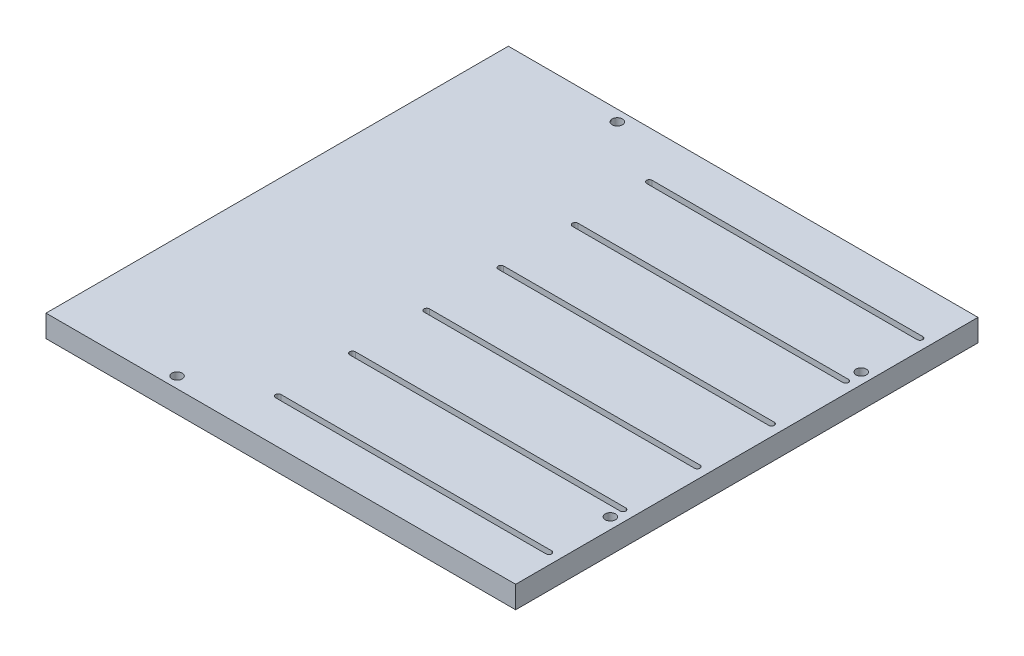
SolidWorks part; units mm, degrees
material "Acrylic (Medium-high impact)"
ref_plane "Front Plane" through (0, 0, 0) normal (0, 0, 1) x (1, 0, 0)
ref_plane "Top Plane" through (0, 0, 0) normal (0, 1, 0) x (1, 0, 0)
ref_plane "Right Plane" through (0, 0, 0) normal (1, 0, 0) x (0, 0, -1)
other "Configuration Table"
sketch "Sketch1" plane through (0, 0, 0) normal (0, 1, 0) x (1, 0, 0)
  line L1 (-42, -66.35) -> (42, -66.35)
  line L2 (-42, -66.35) -> (-42, 66.35) construction
  line L3 (-42, 66.35) -> (42, 66.35)
  line L4 (42, -66.35) -> (42, 66.35)
  line L5 (-42, -66.35) -> (42, 66.35) construction
  line L6 (-42, 66.35) -> (42, -66.35) construction
  line L7 (-42, 66.35) -> (-92.8, 66.35)
  line L9 (-42, -66.35) -> (-92.8, -66.35)
  line L10 (-92.8, 66.35) -> (-92.8, -66.35)
  point P0 (0, 0)
  dimension "D1" = 84
  dimension "D2" = 132.7
  dimension "D3" = 50.8
extrude "Boss-Extrude1" add sketch "Sketch1" along normal blind 6.35
sketch "Sketch2" plane through (0, 6.35, 0) normal (0, 1, 0) x (1, 0, 0)
  line L0 (38.825, -66.35) -> (38.825, 66.35) construction
  line L1 (-92.8, -66.35) -> (42, -66.35) construction
  line L2 (42, 66.35) -> (-92.8, 66.35) construction
  line L3 (42, -66.35) -> (42, 66.35) construction
  line L4 (-42, 0) -> (42, 0) construction
  line L6 (-42, -66.35) -> (-42, 66.35) construction
  circle A0 centre (38.825, -35.997) radius 1.4732
  circle A2 centre (38.825, 35.997) radius 1.4732
  point P12 (0, 0)
  dimension "D2" = 30.353
  dimension "D3" = 2.9464
  dimension "D1" = 3.175
sketch "Sketch4" plane through (0, 6.35, 0) normal (0, 1, 0) x (1, 0, 0)
  point P0 (38.825, 35.997)
  point P3 (38.825, -35.997)
hole_wizard "#4 Clearance Hole1" positions "Sketch4" profile "Sketch5" hole size "#4" standard "ANSI Inch" end condition through all
sketch "Sketch5" plane through (38.825, 6.35, -35.997) normal (1, 0, 0) x (0, 0, 1)
  line L0 (0, 0) -> (0, 6.35)
  line L1 (0, 6.35) -> (1.4732, 6.35)
  line L2 (1.4732, 6.35) -> (1.4732, 0)
  line L5 (1.4732, 0) -> (0, 0)
  line L11 (0, -6.35) -> (0, 107.95) construction
  dimension "Thru Hole Dia." = 2.9464
  dimension "Thru Hole Depth" = 6.35
sketch "Sketch3" plane through (0, 6.35, 0) normal (0, 1, 0) x (1, 0, 0)
  line L0 (-38.825, -53.65) -> (38.825, -53.65) construction
  line L1 (-38.825, -52.8562) -> (38.825, -52.8562)
  line L2 (-38.825, -54.4437) -> (38.825, -54.4437)
  line L3 (-38.825, -53.65) -> (-42, -53.65) construction
  line L4 (-42, -66.35) -> (-42, 66.35) construction
  line L5 (-42, -66.35) -> (42, -66.35) construction
  line L6 (38.825, -53.65) -> (42, -53.65) construction
  line L7 (42, -66.35) -> (42, 66.35) construction
  line L8 (-42, 0) -> (42, 0) construction
  line L9 (-38.825, -32.3487) -> (38.825, -32.3487) construction
  line L10 (-38.825, -31.555) -> (38.825, -31.555)
  line L11 (-38.825, -33.1425) -> (38.825, -33.1425)
  line L12 (-38.825, -11.0475) -> (38.825, -11.0475) construction
  line L13 (-38.825, -10.2537) -> (38.825, -10.2537)
  line L14 (-38.825, -11.8412) -> (38.825, -11.8412)
  line L15 (-38.825, 10.2538) -> (38.825, 10.2538) construction
  line L16 (-38.825, 11.0475) -> (38.825, 11.0475)
  line L17 (-38.825, 9.46) -> (38.825, 9.46)
  line L18 (-38.825, 31.555) -> (38.825, 31.555) construction
  line L19 (-38.825, 32.3488) -> (38.825, 32.3488)
  line L20 (-38.825, 30.7613) -> (38.825, 30.7613)
  line L21 (-38.825, 52.8563) -> (38.825, 52.8563) construction
  line L22 (-38.825, 53.65) -> (38.825, 53.65)
  line L23 (-38.825, 52.0625) -> (38.825, 52.0625)
  line L24 (-42, 66.35) -> (42, 66.35) construction
  arc A0 (-38.825, -52.8562) -> (-38.825, -54.4437) centre (-38.825, -53.65) ccw
  arc A1 (38.825, -54.4437) -> (38.825, -52.8562) centre (38.825, -53.65) ccw
  arc A2 (-38.825, -31.555) -> (-38.825, -33.1425) centre (-38.825, -32.3487) ccw
  arc A3 (38.825, -33.1425) -> (38.825, -31.555) centre (38.825, -32.3487) ccw
  arc A4 (-38.825, -10.2537) -> (-38.825, -11.8412) centre (-38.825, -11.0475) ccw
  arc A5 (38.825, -11.8412) -> (38.825, -10.2537) centre (38.825, -11.0475) ccw
  arc A6 (-38.825, 11.0475) -> (-38.825, 9.46) centre (-38.825, 10.2538) ccw
  arc A7 (38.825, 9.46) -> (38.825, 11.0475) centre (38.825, 10.2538) ccw
  arc A8 (-38.825, 32.3488) -> (-38.825, 30.7613) centre (-38.825, 31.555) ccw
  arc A9 (38.825, 30.7613) -> (38.825, 32.3488) centre (38.825, 31.555) ccw
  arc A10 (-38.825, 53.65) -> (-38.825, 52.0625) centre (-38.825, 52.8563) ccw
  arc A11 (38.825, 52.0625) -> (38.825, 53.65) centre (38.825, 52.8563) ccw
  point P2 (0, -53.65)
  point P22 (0, -32.3487)
  point P29 (0, -11.0475)
  point P36 (0, 10.2538)
  point P43 (0, 31.555)
  point P50 (0, 52.8563)
  dimension "D1" = 1.5875
  dimension "D2" = 3.175
  dimension "D3" = 12.7
  dimension "D4" = 6
  dimension "D5" = 12.7
extrude "Cut-Extrude2" cut sketch "Sketch3" against normal through all
sketch "Sketch6" plane through (0, 0, 0) normal (0, 1, 0) x (1, 0, 0)
  point P0 (-58.35, 63.178)
  point P1 (-58.35, -63.172)
sketch "Sketch7" plane through (0, 6.35, 0) normal (0, 1, 0) x (1, 0, 0)
  point P0 (-58.35, 63.178)
  point P3 (-58.35, -63.172)
hole_wizard "#4 Clearance Hole2" positions "Sketch7" profile "Sketch8" hole size "#4" standard "ANSI Inch"
sketch "Sketch8" plane through (-58.35, 6.35, -63.178) normal (1, 0, 0) x (0, 0, 1)
  line L0 (0, 0) -> (0, 7.2352)
  line L1 (0, 7.2352) -> (1.4732, 6.35)
  line L2 (1.4732, 6.35) -> (1.4732, 0)
  line L5 (1.4732, 0) -> (0, 0)
  line L10 (0, 7.2352) -> (-1.4732, 6.35) construction
  line L11 (0, -6.35) -> (0, 107.95) construction
  dimension "Hole Dia." = 2.9464
  dimension "Hole Depth" = 6.35
  dimension "Drill Angle" = 118
